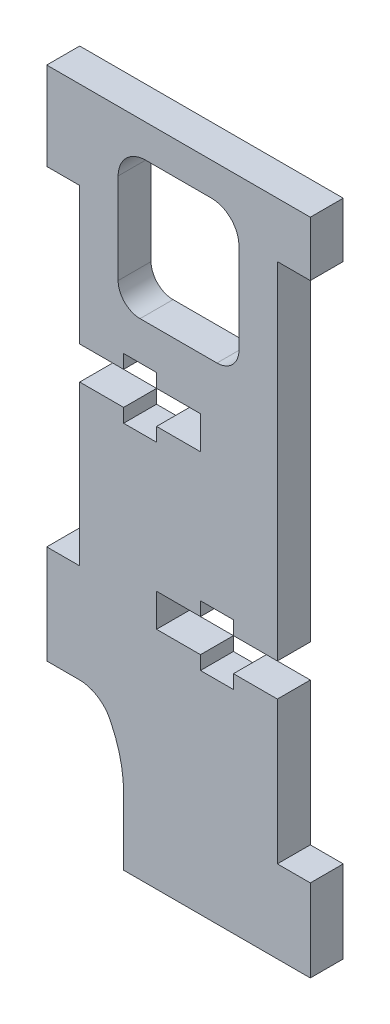
SolidWorks part; units mm, degrees
ref_plane "Front Plane" through (0, 0, 0) normal (0, 0, 1) x (1, 0, 0)
ref_plane "Top Plane" through (0, 0, 0) normal (0, 1, 0) x (1, 0, 0)
ref_plane "Right Plane" through (0, 0, 0) normal (1, 0, 0) x (0, 0, -1)
sketch "Model" plane through (0, 0, 0) normal (0, 0, 1) x (1, 0, 0)
  line L0 (71, 68) -> (71, 63)
  line L1 (61, 44.5) -> (61, 47.5)
  line L2 (50.0235, 21) -> (47, 21)
  line L3 (47, 30) -> (47, 21)
  line L4 (56, 65) -> (62, 65)
  line L5 (55.5, 52.2501) -> (62.5, 52.2501)
  line L6 (53.5, 62.5) -> (53.5, 54.25)
  line L7 (64.5, 62.5) -> (64.5, 54.25)
  line L8 (71, 68) -> (47, 68)
  line L9 (50, 60) -> (47, 60)
  line L10 (61, 47.5) -> (57, 47.5)
  line L11 (61, 44.5) -> (57, 44.5)
  line L12 (54, 47.5) -> (50, 47.5)
  line L13 (54, 44.5) -> (50, 44.5)
  line L14 (50, 30) -> (47, 30)
  line L15 (54, 48.75) -> (54, 47.5)
  line L16 (57, 48.75) -> (57, 47.5)
  line L17 (57, 44.5) -> (57, 43.25)
  line L18 (54, 44.5) -> (54, 43.25)
  line L19 (50, 47.5) -> (50, 60)
  line L20 (50, 44.5) -> (50, 30)
  line L21 (54, 48.75) -> (57, 48.75)
  line L22 (57, 43.25) -> (54, 43.25)
  line L23 (61, 32.75) -> (64, 32.75)
  line L24 (61, 31.5) -> (57, 31.5)
  line L25 (57, 28.5) -> (61, 28.5)
  line L26 (64, 28.5) -> (68, 28.5)
  line L27 (64, 27.25) -> (61, 27.25)
  line L28 (64, 31.5) -> (68, 31.5)
  line L29 (64, 32.75) -> (64, 31.5)
  line L30 (64, 28.5) -> (64, 27.25)
  line L31 (61, 27.25) -> (61, 28.5)
  line L32 (61, 31.5) -> (61, 32.75)
  line L33 (57, 31.5) -> (57, 28.5)
  line L34 (68, 28.5) -> (68, 15.5)
  line L35 (68, 31.5) -> (68, 63)
  line L36 (68, 63) -> (71, 63)
  line L37 (68, 15.5) -> (71, 15.5)
  line L38 (54, 8) -> (71, 8)
  line L39 (54, 14) -> (54, 8)
  line L40 (47, 68) -> (47, 60)
  line L41 (71, 15.5) -> (71, 8)
  arc A0 (56, 65) -> (53.5, 62.5) centre (55.9999, 62.5001) ccw
  arc A1 (53.5, 54.25) -> (55.5, 52.2501) centre (55.4997, 54.2498) ccw
  arc A2 (62.5, 52.2501) -> (64.5, 54.25) centre (62.5001, 54.25) ccw
  arc A3 (64.5, 62.5) -> (62, 65) centre (62, 62.5) ccw
  arc A4 (54, 14) -> (52.861, 19.0467) centre (42.5688, 14.072) ccw
  arc A5 (52.861, 19.0467) -> (50.0235, 21) centre (49.9409, 17.8423) ccw
extrude "Boss-Extrude1" add sketch "Model" along normal blind 3
